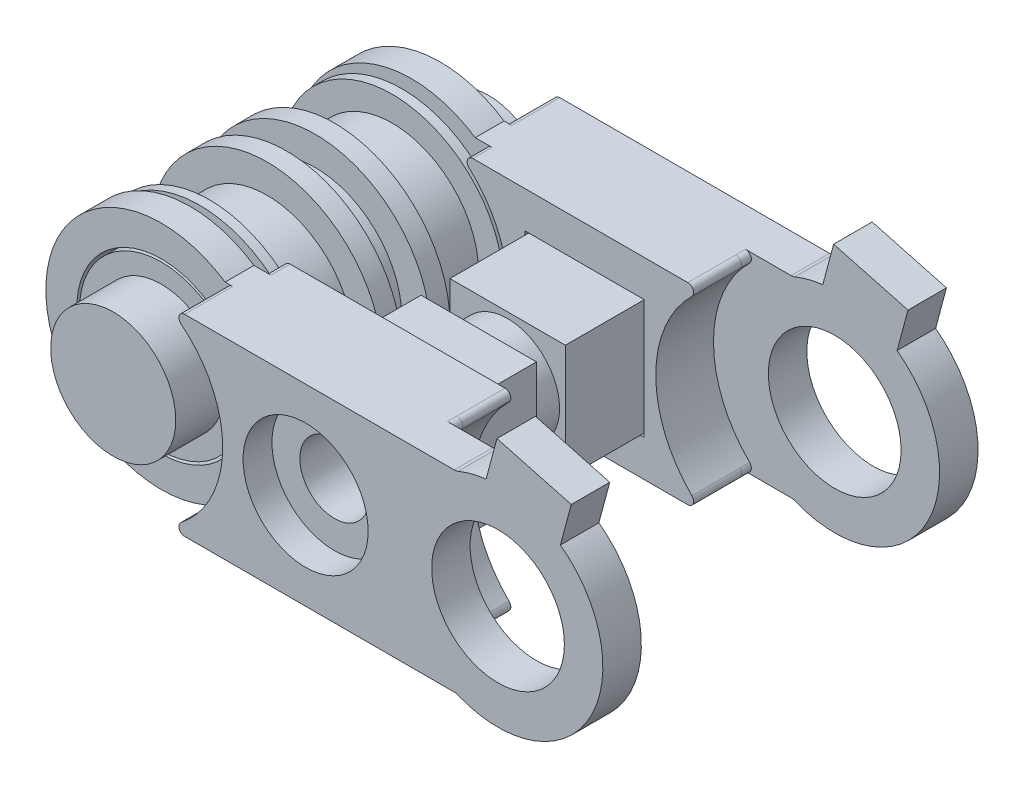
SolidWorks part; units mm, degrees
material "ABS"
ref_plane "正面" through (0, 0, 0) normal (0, 0, 1) x (1, 0, 0)
ref_plane "平面" through (0, 0, 0) normal (0, 1, 0) x (1, 0, 0)
ref_plane "右側面" through (0, 0, 0) normal (1, 0, 0) x (0, 0, -1)
sketch "ｽｹｯﾁ1" plane through (0, 0, 0) normal (0, 0, 1) x (1, 0, 0)
  circle A0 centre (0, 0) radius 4.5
  dimension "D1" = 9
extrude "ﾎﾞｽ - 押し出し1" add sketch "ｽｹｯﾁ1" along normal blind 3
sketch "ｽｹｯﾁ2" plane through (0, 0, 0) normal (0, 0, -1) x (-1, 0, 0)
  circle A0 centre (0, 0) radius 6
  dimension "D1" = 12
extrude "ﾎﾞｽ - 押し出し2" add sketch "ｽｹｯﾁ2" along normal blind 1
sketch "ｽｹｯﾁ3" plane through (0, 0, -1) normal (0, 0, -1) x (-1, 0, 0)
  circle A0 centre (0, 0) radius 4.5 construction
  circle A1 centre (0, 0) radius 4.5
extrude "ﾎﾞｽ - 押し出し3" add sketch "ｽｹｯﾁ3" along normal blind 1.5
sketch "ｽｹｯﾁ4" plane through (0, 0, -2.5) normal (0, 0, -1) x (-1, 0, 0)
  circle A1 centre (0, 0) radius 6
  circle A2 centre (0, 0) radius 6
  dimension "D1" = 0
extrude "ﾎﾞｽ - 押し出し4" add sketch "ｽｹｯﾁ4" along normal blind 1
sketch "ｽｹｯﾁ5" plane through (0, 0, -3.5) normal (0, 0, -1) x (-1, 0, 0)
  circle A0 centre (0, 0) radius 4.5 construction
  circle A1 centre (0, 0) radius 4.5
extrude "ﾎﾞｽ - 押し出し5" add sketch "ｽｹｯﾁ5" along normal blind 3
sketch "ｽｹｯﾁ6" plane through (0, 0, -6.5) normal (0, 0, -1) x (-1, 0, 0)
  circle A1 centre (0, 0) radius 6
  circle A2 centre (0, 0) radius 6
  dimension "D1" = 0
extrude "ﾎﾞｽ - 押し出し6" add sketch "ｽｹｯﾁ6" along normal blind 1
sketch "ｽｹｯﾁ7" plane through (0, 0, 3) normal (0, 0, 1) x (1, 0, 0)
  circle A1 centre (0, 0) radius 6
  circle A2 centre (0, 0) radius 6
  dimension "D1" = 0
extrude "ﾎﾞｽ - 押し出し7" add sketch "ｽｹｯﾁ7" along normal blind 1
sketch "ｽｹｯﾁ10" plane through (0, 0, 4) normal (0, 0, 1) x (1, 0, 0)
  line L1 (3.5, -3.5) -> (-3.5, -3.5) construction
  line L2 (3.5, -3.5) -> (3.5, 3.5) construction
  line L3 (3.5, 3.5) -> (-3.5, 3.5) construction
  line L4 (-3.5, -3.5) -> (-3.5, 3.5) construction
  line L5 (3.5, -3.5) -> (-3.5, 3.5) construction
  line L6 (3.5, 3.5) -> (-3.5, -3.5) construction
  circle A0 centre (0, 0) radius 4.25
  point P0 (0, 0)
  dimension "D3" = 8.5
  dimension "D1" = 7
  dimension "D2" = 7
extrude "ﾎﾞｽ - 押し出し10" add sketch "ｽｹｯﾁ10" along normal blind 1.5
sketch "ｽｹｯﾁ11" plane through (0, 0, 5.5) normal (0, 0, 1) x (1, 0, 0)
  circle A0 centre (0, 0) radius 3.25
  dimension "D1" = 6.5
extrude "ﾎﾞｽ - 押し出し11" add sketch "ｽｹｯﾁ11" along normal blind 2.5
ref_plane "平面1" through (0, 0, -1.75) normal (0, 0, 1) x (1, 0, 0)
mirror "ﾐﾗｰ1" about plane through (0, 0, -1.75) normal (0, 0, 1) of "ﾎﾞｽ - 押し出し11", "ﾎﾞｽ - 押し出し10"
sketch "ｽｹｯﾁ12" plane through (0, 0, 4) normal (0, 0, 1) x (1, 0, 0)
  line L0 (0, 0) -> (20, 0) construction
  line L1 (3.3166, 5) -> (16.1672, 5)
  line L3 (16.1672, -5) -> (3.3166, -5)
  circle A0 centre (0, 0) radius 6 construction
  circle A1 centre (20, 0) radius 3.45 construction
  arc A2 (3.3166, 5) -> (3.3166, -5) centre (0, 0) ccw
  circle A3 centre (20, 0) radius 5.45 construction
  circle A4 centre (20, 0) radius 6.3 construction
  arc A5 (16.1672, 5) -> (16.1672, -5) centre (20, 0) ccw
  circle A6 centre (20, 0) radius 6 construction
  circle A7 centre (0, 0) radius 6 construction
  circle A8 centre (20, 0) radius 3.25 construction
  circle A9 centre (0, 0) radius 3.25 construction
  circle A11 centre (0, 0) radius 4.39
  circle A12 centre (0, 0) radius 4.39
  dimension "D3" = 20
  dimension "D6" = 0.3
  dimension "D2" = 5
  dimension "D7" = 5
  dimension "D4" = 0.2
  dimension "D5" = 2
  dimension "D1" = 0.14
extrude "ﾎﾞｽ - 押し出し12" add sketch "ｽｹｯﾁ12" along normal blind 1.5 separate body
sketch "ｽｹｯﾁ13" plane through (0, 0, 5.5) normal (0, 0, 1) x (1, 0, 0)
  line L6 (16.1672, 5) -> (3.3166, 5) construction
  line L9 (16.1672, 5) -> (3.3166, 5) construction
  line L10 (15.3664, 5) -> (3.7135, 5)
  line L11 (15.3664, -5) -> (3.7135, -5)
  circle A1 centre (0, 0) radius 3.25 construction
  arc A7 (16.1672, 5) -> (16.1672, -5) centre (20, 0) ccw construction
  arc A8 (15.577, 4.4864) -> (15.577, -4.4864) centre (20, 0) ccw
  circle A10 centre (0, 0) radius 5.69 construction
  circle A11 centre (0, 0) radius 3.39 construction
  circle A12 centre (0, 0) radius 5.39 construction
  arc A13 (3.5275, 4.4646) -> (3.5275, -4.4646) centre (0, 0) cw
  arc A14 (15.3664, -5) -> (15.577, -4.4864) centre (15.3664, -4.7) ccw
  arc A15 (15.577, 4.4864) -> (15.3664, 5) centre (15.3664, 4.7) ccw
  arc A16 (3.7135, 5) -> (3.5275, 4.4646) centre (3.7135, 4.7) ccw
  arc A17 (3.5275, -4.4646) -> (3.7135, -5) centre (3.7135, -4.7) ccw
  point P24 (2.7159, 5)
  point P29 (2.7159, -5)
  dimension "D1" = 0.14
  dimension "D3" = 0.3
  dimension "D4" = 2
  dimension "D2" = 0.3
extrude "ﾎﾞｽ - 押し出し13" add sketch "ｽｹｯﾁ13" along normal blind 0.5
fillet "ﾌｨﾚｯﾄ9" radius 0.3 2 edges at (16.1672, -5, 4.75) (16.1672, 5, 4.75)
sketch "ｽｹｯﾁ14" plane through (0, 0, 6) normal (0, 0, 1) x (1, 0, 0)
  line L0 (3.7135, 5) -> (17.7301, 5)
  line L3 (3.7135, -5) -> (17.7301, -5)
  arc A0 (17.7301, 5) -> (17.9208, 5.0378) centre (17.7301, 5.5) ccw
  arc A1 (17.7301, -5) -> (17.9208, -5.0378) centre (17.7301, -5.5) cw
  arc A4 (3.5275, -4.4646) -> (3.7135, -5) centre (3.7135, -4.7) ccw construction
  arc A7 (3.5275, -4.4646) -> (3.5275, 4.4646) centre (0, 0) ccw construction
  arc A8 (3.7135, 5) -> (3.5275, 4.4646) centre (3.7135, 4.7) ccw construction
  arc A9 (3.5275, -4.4646) -> (3.7135, -5) centre (3.7135, -4.7) ccw
  arc A10 (3.7135, 5) -> (3.5275, 4.4646) centre (3.7135, 4.7) ccw
  arc A11 (3.5275, -4.4646) -> (3.5275, 4.4646) centre (0, 0) ccw
  circle A12 centre (20, 0) radius 5.45 construction
  arc A13 (17.9208, 5.0378) -> (17.9208, -5.0378) centre (20, 0) cw
  circle A14 centre (20, 0) radius 3.45 construction
  circle A15 centre (20, 0) radius 3.45
  point P19 (17.8315, -5)
  point P22 (17.8315, 5)
  point P24 (17.8315, 5)
  point P27 (17.8315, -5)
  dimension "D1" = 0.5
extrude "ﾎﾞｽ - 押し出し14" add sketch "ｽｹｯﾁ14" along normal blind 2
sketch "ｽｹｯﾁ15" plane through (0, 0, 4) normal (0, 0, -1) x (-1, 0, 0)
  line L0 (-15.3664, 5) -> (-4.1952, 5)
  line L1 (-3.3166, 5) -> (-16.1672, 5) construction
  line L2 (-15.3664, -5) -> (-4.1952, -5)
  line L3 (-16.1672, -5) -> (-3.3166, -5) construction
  circle A2 centre (0, 0) radius 6 construction
  arc A3 (-3.9955, 4.4762) -> (-3.9955, -4.4762) centre (0, 0) ccw
  arc A7 (-4.1952, -5) -> (-3.9955, -4.4762) centre (-4.1952, -4.7) ccw
  arc A8 (-4.1952, 5) -> (-3.9955, 4.4762) centre (-4.1952, 4.7) cw
  arc A10 (-15.577, -4.4864) -> (-15.3664, -5) centre (-15.3664, -4.7) ccw construction
  arc A11 (-15.577, -4.4864) -> (-15.577, 4.4864) centre (-20, 0) ccw construction
  arc A12 (-15.3664, 5) -> (-15.577, 4.4864) centre (-15.3664, 4.7) ccw construction
  arc A13 (-15.577, -4.4864) -> (-15.3664, -5) centre (-15.3664, -4.7) ccw
  arc A14 (-15.577, -4.4864) -> (-15.577, 4.4864) centre (-20, 0) ccw
  arc A15 (-15.3664, 5) -> (-15.577, 4.4864) centre (-15.3664, 4.7) ccw
  point P26 (-3.3166, -5)
  point P29 (-3.3166, 5)
  dimension "D2" = 0.3
extrude "ﾎﾞｽ - 押し出し15" add sketch "ｽｹｯﾁ15" along normal blind 1
mirror "ﾐﾗｰ2" about plane through (0, 0, -1.75) normal (0, 0, 1) of bodies 116
sketch "ｽｹｯﾁ16" plane through (0, 0, 8) normal (0, 0, 1) x (1, 0, 0)
  line L0 (0, 0) -> (20, 0) construction
  circle A0 centre (20, 0) radius 3.45 construction
  circle A1 centre (10, 0) radius 1.8
  dimension "D1" = 3.6
extrude "ｶｯﾄ - 押し出し1" cut sketch "ｽｹｯﾁ16" against normal through all
sketch "ｽｹｯﾁ17" plane through (0, 0, -6.5) normal (0, 0, 1) x (1, 0, 0)
  line L1 (13.1, -3.1) -> (6.9, -3.1)
  line L2 (13.1, -3.1) -> (13.1, 3.1)
  line L3 (13.1, 3.1) -> (6.9, 3.1)
  line L4 (6.9, -3.1) -> (6.9, 3.1)
  line L5 (13.1, -3.1) -> (6.9, 3.1) construction
  line L6 (13.1, 3.1) -> (6.9, -3.1) construction
  point P0 (10, 0)
  dimension "D2" = 6.2
  dimension "D1" = 6.2
extrude "ｶｯﾄ - 押し出し2" cut sketch "ｽｹｯﾁ17" against normal blind 2
sketch "ｽｹｯﾁ18" plane through (0, 0, 3) normal (0, 0, -1) x (-1, 0, 0)
  line L0 (-7, 3) -> (-13, 3)
  line L5 (-13, 3) -> (-13, -3)
  line L6 (-13, -3) -> (-7, -3)
  line L7 (-7, -3) -> (-7, 3)
  line L8 (-13.1, -3.1) -> (-6.9, -3.1)
  line L9 (-6.9, -3.1) -> (-6.9, 3.1)
  line L10 (-6.9, 3.1) -> (-13.1, 3.1)
  line L11 (-13.1, 3.1) -> (-13.1, -3.1)
  line L12 (-13.1, -3.1) -> (-6.9, -3.1) construction
  line L13 (-6.9, -3.1) -> (-6.9, 3.1) construction
  line L14 (-6.9, 3.1) -> (-13.1, 3.1) construction
  line L15 (-13.1, 3.1) -> (-13.1, -3.1) construction
  dimension "D1" = 0
  dimension "D2" = 0.1
extrude "ﾎﾞｽ - 押し出し16" add sketch "ｽｹｯﾁ18" along normal up to surface (11.5 mm away) up to face at (10, 0, -8.5)
sketch "ｽｹｯﾁ19" plane through (0, 0, 3) normal (0, 0, 1) x (1, 0, 0)
  circle A0 centre (10, 0) radius 1.8 construction
  circle A1 centre (10, 0) radius 1.8
extrude "ｶｯﾄ - 押し出し3" cut sketch "ｽｹｯﾁ19" against normal through all
sketch "ｽｹｯﾁ20" plane through (0, 0, -1.75) normal (0, 0, 1) x (1, 0, 0)
  line L4 (13, 3) -> (7, 3)
  line L5 (13, -3) -> (13, 3)
  line L6 (7, -3) -> (13, -3)
  line L7 (7, 3) -> (7, -3)
  line L8 (13, 3) -> (7, 3)
  line L9 (13, -3) -> (13, 3)
  line L10 (7, -3) -> (13, -3)
  line L11 (7, 3) -> (7, -3)
  circle A1 centre (10, 0) radius 2.7
  dimension "D2" = 5.4
  dimension "D1" = 0
extrude "ｶｯﾄ - 押し出し4" cut sketch "ｽｹｯﾁ20" against normal blind 0.75 and the other way blind 0.75
sketch "ｽｹｯﾁ21" plane through (0, 0, 8) normal (0, 0, 1) x (1, 0, 0)
  circle A0 centre (10, 0) radius 3.25
  dimension "D1" = 6.5
extrude "ｶｯﾄ - 押し出し5" cut sketch "ｽｹｯﾁ21" against normal blind 1.5
sketch "ｽｹｯﾁ22" plane through (0, 0, -11.5) normal (0, 0, -1) x (-1, 0, 0)
  line L1 (-11.6743, 2.9) -> (-13.3486, 0)
  line L2 (-13.3486, 0) -> (-11.6743, -2.9)
  line L3 (-11.6743, -2.9) -> (-8.3257, -2.9)
  line L4 (-8.3257, -2.9) -> (-6.6514, 0)
  line L5 (-6.6514, 0) -> (-8.3257, 2.9)
  line L6 (-8.3257, 2.9) -> (-11.6743, 2.9)
  circle A0 centre (-10, 0) radius 2.9 construction
  dimension "D1" = 5.8
extrude "ｶｯﾄ - 押し出し6" cut sketch "ｽｹｯﾁ22" against normal blind 1
sketch "ｽｹｯﾁ23" plane through (0, 0, 8) normal (0, 0, 1) x (1, 0, 0)
  line L0 (20, 0) -> (21.4106, 5.2643) construction
  line L1 (19.0128, 4.0433) -> (22.8765, 3.008)
  line L2 (19.0128, 4.0433) -> (19.9446, 7.5206)
  line L3 (19.9446, 7.5206) -> (23.8083, 6.4853)
  line L4 (22.8765, 3.008) -> (23.8083, 6.4853)
  line L5 (19.0128, 4.0433) -> (23.8083, 6.4853) construction
  line L6 (19.9446, 7.5206) -> (22.8765, 3.008) construction
  line L7 (20, 0) -> (20, 5.45) construction
  arc A0 (17.9208, -5.0378) -> (17.9208, 5.0378) centre (20, 0) ccw construction
  point P0 (21.4106, 5.2643)
  dimension "D1" = 1.8
  dimension "D2" = 4
  dimension "D3" = 15
extrude "ﾎﾞｽ - 押し出し17" add sketch "ｽｹｯﾁ23" against normal up to surface (2 mm away) up to face at (17.3986, 0, 6)
sketch "ｽｹｯﾁ24" plane through (0, 0, -11.5) normal (0, 0, -1) x (-1, 0, 0)
  line L4 (-22.8765, 3.008) -> (-19.0128, 4.0433)
  line L5 (-23.8083, 6.4853) -> (-22.8765, 3.008)
  line L6 (-19.9446, 7.5206) -> (-23.8083, 6.4853)
  line L7 (-19.0128, 4.0433) -> (-19.9446, 7.5206)
  line L8 (-22.8765, 3.008) -> (-19.0128, 4.0433)
  line L9 (-23.8083, 6.4853) -> (-22.8765, 3.008)
  line L10 (-19.9446, 7.5206) -> (-23.8083, 6.4853)
  line L11 (-19.0128, 4.0433) -> (-19.9446, 7.5206)
  dimension "D1" = 0
extrude "ﾎﾞｽ - 押し出し18" add sketch "ｽｹｯﾁ24" against normal up to surface (2 mm away) up to face at (17.3986, 0, -9.5)
ref_plane "平面2" through (-4.5, 0, 0) normal (-1, 0, 0) x (0, 0, 1)
sketch "ｽｹｯﾁ25" plane through (-4.5, 0, 0) normal (-1, 0, 0) x (0, 0, 1)
  line L0 (-6.5, 0) -> (3, 0) construction
  line L1 (-6.5, -4.5) -> (-6.5, 4.5) construction
  line L2 (3, 4.5) -> (3, -4.5) construction
  line L3 (-3.5, 4.5) -> (-3.5, -4.5) construction
  line L4 (-6.5, -1) -> (-3.5, -1)
  line L5 (-6.5, -1) -> (-6.5, 1)
  line L6 (-6.5, 1) -> (-3.5, 1)
  line L7 (-3.5, -1) -> (-3.5, 1)
  line L8 (0, -4.5) -> (0, 4.5) construction
  line L9 (0, -1) -> (3, -1)
  line L10 (0, -1) -> (0, 1)
  line L11 (0, 1) -> (3, 1)
  line L12 (3, -1) -> (3, 1)
  line L13 (3, 6) -> (3, -6) construction
  dimension "D1" = 2
  dimension "D2" = 1
extrude "ｶｯﾄ - 押し出し7" [suppressed] cut sketch "ｽｹｯﾁ25" against normal through all
fillet "ﾌｨﾚｯﾄ10" [suppressed] radius 0.5
sketch "ｽｹｯﾁ26" plane through (0, 0, 3) normal (0, 0, -1) x (-1, 0, 0)
  circle A2 centre (0, 0) radius 5.8
  circle A3 centre (0, 0) radius 5.8
  circle A4 centre (0, 0) radius 6
  circle A5 centre (0, 0) radius 6
  dimension "D1" = 0.2
  dimension "D2" = 0
extrude "ｶｯﾄ - 押し出し8" cut sketch "ｽｹｯﾁ26" against normal through all
sketch "ｽｹｯﾁ27" plane through (0, 0, -6.5) normal (0, 0, 1) x (1, 0, 0)
  circle A1 centre (0, 0) radius 6
  circle A2 centre (0, 0) radius 6
  circle A3 centre (0, 0) radius 5.8
  circle A4 centre (0, 0) radius 5.8
  dimension "D1" = 0
  dimension "D2" = 0
extrude "ｶｯﾄ - 押し出し9" cut sketch "ｽｹｯﾁ27" against normal through all
sketch "ｽｹｯﾁ28" plane through (0, 0, 4) normal (0, 0, -1) x (-1, 0, 0)
  circle A0 centre (0, 0) radius 4.25 construction
  circle A1 centre (0, 0) radius 5.8
  circle A2 centre (0, 0) radius 5.8
  circle A3 centre (0, 0) radius 4.25
  dimension "D1" = 0
extrude "ｶｯﾄ - 押し出し10" cut sketch "ｽｹｯﾁ28" along normal blind 0.5
sketch "ｽｹｯﾁ29" plane through (0, 0, -7.5) normal (0, 0, 1) x (1, 0, 0)
  circle A1 centre (0, 0) radius 4.25
  circle A2 centre (0, 0) radius 4.25
  circle A3 centre (0, 0) radius 5.8
  circle A4 centre (0, 0) radius 5.8
  dimension "D1" = 0
  dimension "D2" = 0
extrude "ｶｯﾄ - 押し出し11" cut sketch "ｽｹｯﾁ29" along normal blind 0.5
equation "\"D7@ｽｹｯﾁ12\"=\"D2@ｽｹｯﾁ12\""
equation "\"D1@ｽｹｯﾁ17\"=\"D2@ｽｹｯﾁ17\""
equation "\"D2@ｽｹｯﾁ25\"=\"D1@ｽｹｯﾁ25\"/2"
